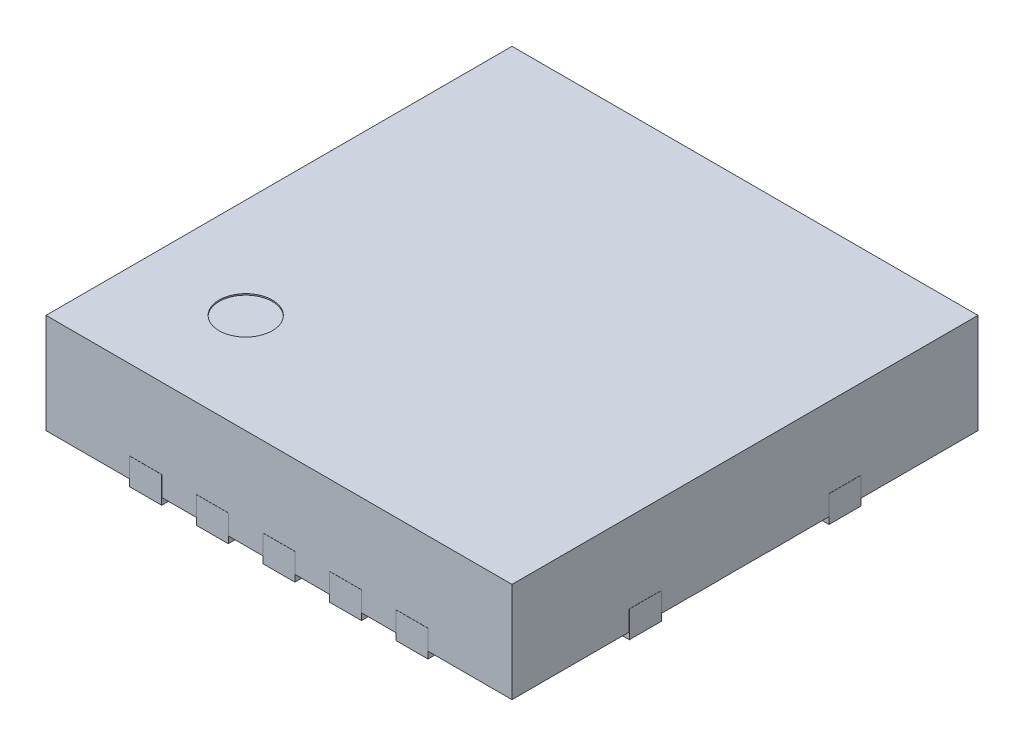
SolidWorks part; units mm, degrees
ref_plane "Front Plane" through (0, 0, 0) normal (0, 0, 1) x (1, 0, 0)
ref_plane "Top Plane" through (0, 0, 0) normal (0, 1, 0) x (1, 0, 0)
ref_plane "Right Plane" through (0, 0, 0) normal (1, 0, 0) x (0, 0, -1)
sketch "Sketch1" plane through (0, 0, 0) normal (0, 1, 0) x (1, 0, 0)
  line L1 (-1.75, -1.75) -> (1.75, -1.75)
  line L2 (-1.75, -1.75) -> (-1.75, 1.75)
  line L3 (-1.75, 1.75) -> (1.75, 1.75)
  line L4 (1.75, -1.75) -> (1.75, 1.75)
  line L5 (-1.75, -1.75) -> (1.75, 1.75) construction
  line L6 (-1.75, 1.75) -> (1.75, -1.75) construction
  point P0 (0, 0)
  dimension "D1" = 3.5
  dimension "D2" = 3.5
extrude "Boss-Extrude1" add sketch "Sketch1" along normal blind 0.75
sketch "Sketch2" plane through (0, 0.75, 0) normal (0, 1, 0) x (1, 0, 0)
  circle A0 centre (-1, -1) radius 0.2
  dimension "D1" = 1
  dimension "D2" = 1
extrude "Cut-Extrude1" cut sketch "Sketch2" against normal blind 0.01
sketch "Sketch3" plane through (0, 0, 0) normal (0, -1, 0) x (1, 0, 0)
  line L0 (-1.75, 0) -> (1.75, 0) construction
  line L1 (-1.12, 1.751) -> (-0.88, 1.751)
  line L2 (-1.12, 1.751) -> (-1.12, 1.471)
  line L3 (-1.75, -1.75) -> (-1.75, 1.75) construction
  line L4 (-0.88, 1.751) -> (-0.88, 1.471)
  line L5 (1.75, 1.75) -> (1.75, -1.75) construction
  line L6 (-1.751, 0.63) -> (-1.751, 0.87)
  line L7 (-1.751, 0.87) -> (-1.471, 0.87)
  line L8 (-1.751, 0.63) -> (-1.471, 0.63)
  line L9 (-0.62, 1.751) -> (-0.62, 1.471)
  line L10 (-0.38, 1.751) -> (-0.38, 1.471)
  line L11 (-0.62, 1.751) -> (-0.38, 1.751)
  line L12 (-0.12, 1.751) -> (-0.12, 1.471)
  line L13 (0.12, 1.751) -> (0.12, 1.471)
  line L14 (-0.12, 1.751) -> (0.12, 1.751)
  line L15 (0.38, 1.751) -> (0.38, 1.471)
  line L16 (0.62, 1.751) -> (0.62, 1.471)
  line L17 (0.38, 1.751) -> (0.62, 1.751)
  line L18 (0.88, 1.751) -> (0.88, 1.471)
  line L19 (0, 1.75) -> (0, -1.75) construction
  line L20 (-1.75, 1.75) -> (1.75, 1.75) construction
  line L21 (1.75, -1.75) -> (-1.75, -1.75) construction
  line L22 (1.12, 1.751) -> (1.12, 1.471)
  line L23 (0.88, 1.751) -> (1.12, 1.751)
  line L24 (1.751, -0.63) -> (1.751, -0.87)
  line L25 (1.751, -0.87) -> (1.471, -0.87)
  line L26 (1.751, -0.63) -> (1.471, -0.63)
  line L27 (0.88, -1.751) -> (1.12, -1.751)
  line L28 (1.12, -1.751) -> (1.12, -1.471)
  line L29 (0.88, -1.751) -> (0.88, -1.471)
  line L30 (0.38, -1.751) -> (0.62, -1.751)
  line L31 (0.62, -1.751) -> (0.62, -1.471)
  line L32 (0.38, -1.751) -> (0.38, -1.471)
  line L33 (-0.12, -1.751) -> (0.12, -1.751)
  line L34 (0.12, -1.751) -> (0.12, -1.471)
  line L35 (-0.12, -1.751) -> (-0.12, -1.471)
  line L36 (-0.62, -1.751) -> (-0.38, -1.751)
  line L37 (-0.38, -1.751) -> (-0.38, -1.471)
  line L38 (-0.62, -1.751) -> (-0.62, -1.471)
  line L39 (-1.751, -0.63) -> (-1.471, -0.63)
  line L40 (-1.751, -0.87) -> (-1.471, -0.87)
  line L41 (-1.751, -0.63) -> (-1.751, -0.87)
  line L42 (-0.88, -1.751) -> (-0.88, -1.471)
  line L43 (-1.12, -1.751) -> (-1.12, -1.471)
  line L44 (-1.12, -1.751) -> (-0.88, -1.751)
  line L45 (1.751, 0.63) -> (1.471, 0.63)
  line L46 (1.751, 0.87) -> (1.471, 0.87)
  line L47 (1.751, 0.63) -> (1.751, 0.87)
  arc A0 (-0.88, 1.471) -> (-1.12, 1.471) centre (-1, 1.471) cw
  arc A1 (-1.471, 0.87) -> (-1.471, 0.63) centre (-1.471, 0.75) cw
  arc A2 (-0.38, 1.471) -> (-0.62, 1.471) centre (-0.5, 1.471) cw
  arc A3 (0.12, 1.471) -> (-0.12, 1.471) centre (0, 1.471) cw
  arc A4 (0.62, 1.471) -> (0.38, 1.471) centre (0.5, 1.471) cw
  arc A5 (1.12, 1.471) -> (0.88, 1.471) centre (1, 1.471) cw
  arc A6 (1.471, -0.87) -> (1.471, -0.63) centre (1.471, -0.75) cw
  arc A7 (1.12, -1.471) -> (0.88, -1.471) centre (1, -1.471) ccw
  arc A8 (0.62, -1.471) -> (0.38, -1.471) centre (0.5, -1.471) ccw
  arc A9 (0.12, -1.471) -> (-0.12, -1.471) centre (0, -1.471) ccw
  arc A10 (-0.38, -1.471) -> (-0.62, -1.471) centre (-0.5, -1.471) ccw
  arc A11 (-1.471, -0.87) -> (-1.471, -0.63) centre (-1.471, -0.75) ccw
  arc A12 (-0.88, -1.471) -> (-1.12, -1.471) centre (-1, -1.471) ccw
  arc A13 (1.471, 0.87) -> (1.471, 0.63) centre (1.471, 0.75) ccw
  dimension "D7" = 0.001
  dimension "D4" = 0.12
  dimension "D9" = 0.12
  dimension "D11" = 0.28
  dimension "D1" = 0.24
  dimension "D2" = 0.28
  dimension "D3" = 1
  dimension "D5" = 0.001
  dimension "D6" = 0.75
  dimension "D8" = 0.28
  dimension "D10" = 0.28
  dimension "D12" = 0.24
  dimension "D13" = 0.12
extrude "Boss-Extrude2" add sketch "Sketch3" along normal blind 0.05 and the other way blind 0.15
sketch "Sketch4" plane through (0, 0, 0) normal (0, -1, 0) x (1, 0, 0)
  line L0 (-1, 0.6) -> (-0.6, 1)
  line L1 (-1, -1) -> (1, -1)
  line L2 (-1, -1) -> (-1, -0.375)
  line L3 (-0.6, 1) -> (1, 1)
  line L4 (1, -1) -> (1, -0.375)
  line L5 (-1.75, 0) -> (-1.4696, 0) construction
  line L6 (-1.75, -0.63) -> (-1.75, 0.63) construction
  line L8 (-1, 0.375) -> (-1, 0.6)
  line L9 (0, 1.751) -> (0, -1.751) construction
  line L10 (-1.75, 0.175) -> (-1.4696, 0.175)
  line L11 (-1.75, -0.375) -> (-1, -0.375)
  line L12 (-1.75, 0.375) -> (-1, 0.375)
  line L13 (-1.75, -0.175) -> (-1.4696, -0.175)
  line L14 (-1.4696, 0.175) -> (-1.4696, -0.175)
  line L15 (0.12, 1.751) -> (-0.12, 1.751) construction
  line L16 (-0.12, -1.751) -> (0.12, -1.751) construction
  line L17 (-1.75, 0.375) -> (-1.75, 0.175)
  line L18 (-1.75, -0.175) -> (-1.75, -0.375)
  line L19 (1.75, -0.375) -> (1, -0.375)
  line L20 (1.75, 0) -> (1.4696, 0) construction
  line L21 (1.75, -0.175) -> (1.75, -0.375)
  line L22 (1.4696, 0.175) -> (1.4696, -0.175)
  line L23 (1.75, -0.175) -> (1.4696, -0.175)
  line L24 (1.75, 0.175) -> (1.4696, 0.175)
  line L25 (1.75, 0.375) -> (1.75, 0.175)
  line L26 (1.75, 0.375) -> (1, 0.375)
  line L27 (1, 0.375) -> (1, 1)
  point P0 (0, 0)
  point P3 (-1, 1)
  dimension "D1" = 2
  dimension "D2" = 2
extrude "Boss-Extrude3" add sketch "Sketch4" along normal blind 0.001
